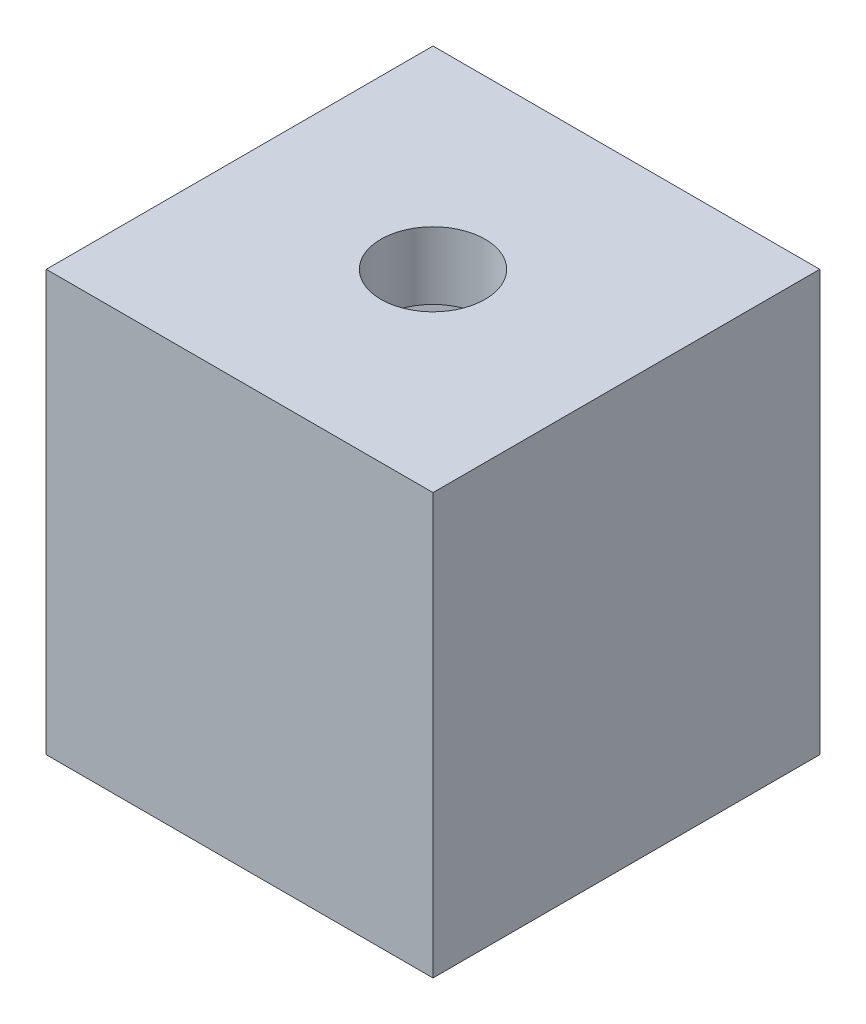
SolidWorks part; units mm, degrees
ref_plane "Front Plane" through (0, 0, 0) normal (0, 0, 1) x (1, 0, 0)
ref_plane "Top Plane" through (0, 0, 0) normal (0, 1, 0) x (1, 0, 0)
ref_plane "Right Plane" through (0, 0, 0) normal (1, 0, 0) x (0, 0, -1)
sketch "Sketch3" plane through (0, 0, 0) normal (0, 1, 0) x (1, 0, 0)
  line L1 (-5.75, -5.75) -> (5.75, -5.75)
  line L2 (-5.75, -5.75) -> (-5.75, 5.75)
  line L3 (-5.75, 5.75) -> (5.75, 5.75)
  line L4 (5.75, -5.75) -> (5.75, 5.75)
  line L5 (-5.75, -5.75) -> (5.75, 5.75) construction
  line L6 (-5.75, 5.75) -> (5.75, -5.75) construction
  point P0 (0, 0)
  dimension "D1" = 11.5
  dimension "D2" = 11.5
extrude "Boss-Extrude1" add sketch "Sketch3" along normal blind 12.5 contours L2 L1 L4 L3
ref_plane "Plane1" through (0, 10.5, 0) normal (0, 1, 0) x (1, 0, 0)
sketch "Sketch4" plane through (0, 10.5, 0) normal (0, 1, 0) x (1, 0, 0)
  circle A0 centre (0, 0) radius 1.55
  dimension "D1" = 3.1
extrude "Cut-Extrude1" cut sketch "Sketch4" along normal through all
sketch "Sketch5" plane through (0, 10.5, 0) normal (0, 1, 0) x (1, 0, 0)
  line L1 (3.06, 0) -> (1.53, 2.65)
  line L2 (1.53, 2.65) -> (-1.53, 2.65)
  line L3 (-1.53, 2.65) -> (-3.06, 0)
  line L4 (-3.06, 0) -> (-1.53, -2.65)
  line L5 (-1.53, -2.65) -> (1.53, -2.65)
  line L6 (1.53, -2.65) -> (3.06, 0)
  circle A0 centre (0, 0) radius 2.65 construction
  dimension "D1" = 5.3
extrude "Cut-Extrude2" cut sketch "Sketch5" against normal through all
sketch "Sketch6" plane through (0, 0, 0) normal (1, 0, 0) x (0, 0, -1)
  line L0 (0, 0) -> (0, 12.9621) construction
  line L2 (-2.65, 0) -> (2.65, 0)
  line L3 (-2.65, 0) -> (-2.65, 10.5)
  line L4 (-2.65, 10.5) -> (2.65, 10.5)
  line L5 (2.65, 0) -> (2.65, 10.5)
  line L6 (-2.65, 0) -> (2.65, 10.5) construction
  line L7 (-2.65, 10.5) -> (2.65, 0) construction
  line L8 (-5.75, 0) -> (5.75, 0) construction
  line L9 (6.325, 10.5) -> (-6.325, 10.5) construction
  point P3 (0, 5.25)
  dimension "D1" = 5.3
extrude "Cut-Extrude3" cut sketch "Sketch6" against normal through all
